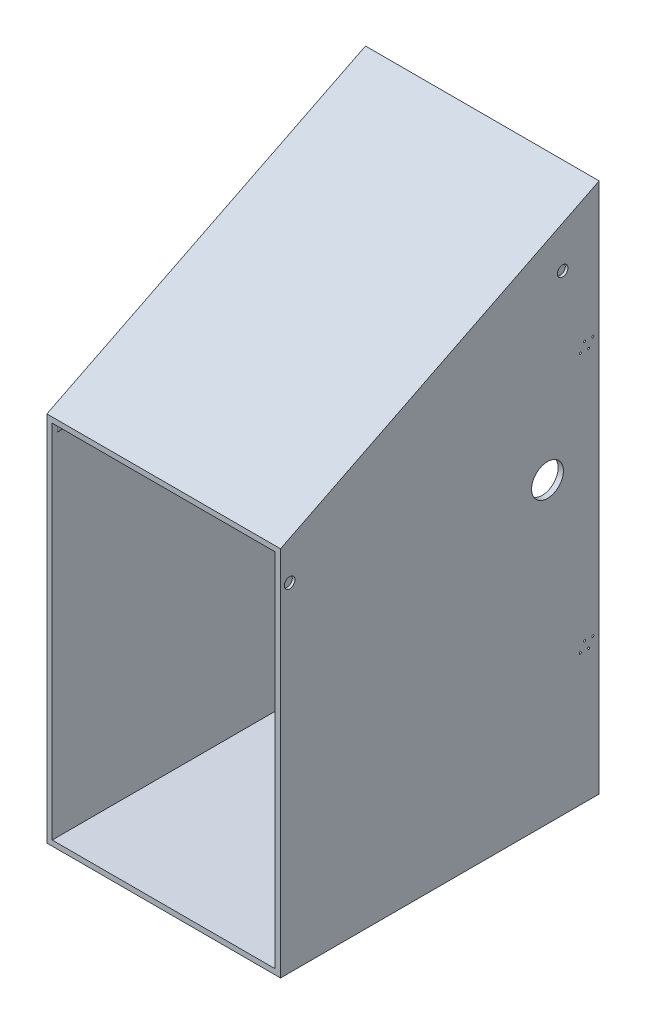
SolidWorks part; units mm, degrees
ref_plane "Front Plane" through (0, 0, 0) normal (0, 0, 1) x (1, 0, 0)
ref_plane "Top Plane" through (0, 0, 0) normal (0, 1, 0) x (1, 0, 0)
ref_plane "Right Plane" through (0, 0, 0) normal (1, 0, 0) x (0, 0, -1)
sketch "Sketch1" plane through (0, 0, 0) normal (0, 0, 1) x (1, 0, 0)
  line L1 (0, 0) -> (558.8, 0)
  line L2 (0, 0) -> (0, 889)
  line L3 (0, 889) -> (558.8, 889)
  line L4 (558.8, 0) -> (558.8, 889)
  dimension "D1" = 558.8
  dimension "D2" = 889
extrude "Boss-Extrude1" add sketch "Sketch1" along normal blind 762
sketch "Sketch3" plane through (558.8, 0, 0) normal (1, 0, 0) x (0, 0, -1)
  line L0 (0, 889) -> (0, 1270)
  line L1 (0, 1270) -> (-762, 889)
  line L2 (-762, 889) -> (0, 889)
  dimension "D1" = 381
extrude "Boss-Extrude2" add sketch "Sketch3" against normal blind 558.8
sketch "Sketch4" plane through (0, 0, 762) normal (0, 0, 1) x (1, 0, 0)
  line L0 (0, 0) -> (558.8, 0) construction
  line L1 (12.7, 12.7) -> (546.1, 12.7)
  line L2 (12.7, 12.7) -> (12.7, 139.7)
  line L3 (12.7, 139.7) -> (546.1, 139.7)
  line L4 (546.1, 12.7) -> (546.1, 139.7)
  line L5 (0, 889) -> (0, 0) construction
  line L6 (558.8, 0) -> (558.8, 889) construction
  dimension "D1" = 127
  dimension "D2" = 12.7
  dimension "D3" = 12.7
  dimension "D4" = 12.7
extrude "Cut-Extrude1" cut sketch "Sketch4" against normal through all
sketch "Sketch5" plane through (0, 0, 762) normal (0, 0, 1) x (1, 0, 0)
  line L0 (558.8, 889) -> (0, 889) construction
  line L1 (12.7, 152.4) -> (546.1, 152.4)
  line L2 (12.7, 152.4) -> (12.7, 876.3)
  line L3 (12.7, 876.3) -> (546.1, 876.3)
  line L4 (546.1, 152.4) -> (546.1, 876.3)
  line L5 (546.1, 139.7) -> (12.7, 139.7) construction
  line L6 (0, 889) -> (0, 0) construction
  line L7 (558.8, 0) -> (558.8, 889) construction
  dimension "D1" = 12.7
  dimension "D2" = 12.7
  dimension "D3" = 12.7
  dimension "D4" = 12.7
extrude "Cut-Extrude3" cut sketch "Sketch5" against normal blind 755.142
sketch "Sketch6" plane through (0, 0, 0) normal (0, 0, -1) x (-1, 0, 0)
  line L0 (0, 1270) -> (-558.8, 1270) construction
  line L5 (-558.8, 0) -> (-558.8, 1270) construction
  line L6 (-546.1, 1244.6) -> (-12.7, 1244.6)
  line L7 (-546.1, 1244.6) -> (-546.1, 355.6)
  line L8 (-546.1, 355.6) -> (-12.7, 355.6)
  line L9 (-12.7, 1244.6) -> (-12.7, 355.6)
  line L10 (0, 1270) -> (0, 0) construction
  dimension "D1" = 889
  dimension "D2" = 25.4
  dimension "D3" = 12.7
  dimension "D4" = 12.7
extrude "Cut-Extrude4" cut sketch "Sketch6" against normal blind 10.16
sketch "Sketch7" plane through (0, 0, 0) normal (-1, 0, 0) x (0, 0, 1)
  line L0 (762, 0) -> (0, 0) construction
  line L1 (0, 1270) -> (0, 0) construction
  circle A0 centre (123.444, 712.216) radius 38.1
  dimension "D1" = 76.2
  dimension "D2" = 712.216
  dimension "D3" = 123.444
extrude "Cut-Extrude5" cut sketch "Sketch7" against normal through all
sketch "Sketch11" plane through (546.1, 0, 0) normal (-1, 0, 0) x (0, 0, 1)
  line L0 (0, 880.8771) -> (0, 1247.6567)
  line L1 (0, 1270) -> (0, 0) construction
  line L2 (0, 1247.6567) -> (749.8476, 880.8771)
  line L4 (0, 1270) -> (762, 889) construction
  line L5 (749.8476, 880.8771) -> (749.8476, 851.3755)
  line L6 (749.8476, 851.3755) -> (0, 851.3755)
  line L7 (0, 851.3755) -> (0, 880.8771)
  dimension "D1" = 0.5
  dimension "D2" = 12.7
  dimension "D3" = 366.7796
extrude "Cut-Extrude6" cut sketch "Sketch11" along normal blind 533.908
sketch "Sketch12" plane through (0, 0, 762) normal (0, 0, 1) x (1, 0, 0)
  line L1 (12.7, 152.4) -> (546.1, 152.4)
  line L2 (12.7, 152.4) -> (12.7, 139.7)
  line L3 (12.7, 139.7) -> (546.1, 139.7)
  line L4 (546.1, 152.4) -> (546.1, 139.7)
extrude "Cut-Extrude7" cut sketch "Sketch12" against normal up to next
sketch "Sketch13" plane through (0, 0, 0) normal (-1, 0, 0) x (0, 0, 1)
  circle A0 centre (45, 955.2066) radius 2.5
  circle A1 centre (25, 955.2066) radius 2.5
  circle A2 centre (35, 935.2066) radius 2.5
  circle A3 centre (15, 935.2066) radius 2.5
  circle A4 centre (740.166, 807.8545) radius 12.7
  circle A5 centre (35, 314.7934) radius 2.5
  circle A6 centre (45, 334.7934) radius 2.5
  circle A7 centre (25, 334.7934) radius 2.5
  circle A8 centre (15, 314.7934) radius 2.5
extrude "Boss-Extrude3" add sketch "Sketch13" along normal blind 6.35
sketch "Sketch14" plane through (558.8, 0, 0) normal (1, 0, 0) x (0, 0, -1)
  circle A0 centre (-87.3097, 1127.1918) radius 12.7
  circle A1 centre (-740.166, 807.8545) radius 12.7
  circle A2 centre (-25, 935.2066) radius 2.5
  circle A3 centre (-45, 935.2066) radius 2.5
  circle A4 centre (-35, 955.2066) radius 2.5
  circle A5 centre (-15, 955.2066) radius 2.5
  circle A6 centre (-25, 314.7934) radius 2.5
  circle A7 centre (-45, 314.7934) radius 2.5
  circle A8 centre (-35, 334.7934) radius 2.5
  circle A9 centre (-15, 334.7934) radius 2.5
extrude "Cut-Extrude8" cut sketch "Sketch14" against normal blind 6.35
sketch "Sketch15" plane through (0, 0, 0) normal (-1, 0, 0) x (0, 0, 1)
  circle A0 centre (87.3097, 1127.1918) radius 12.7
extrude "Cut-Extrude9" cut sketch "Sketch15" against normal blind 6.35
